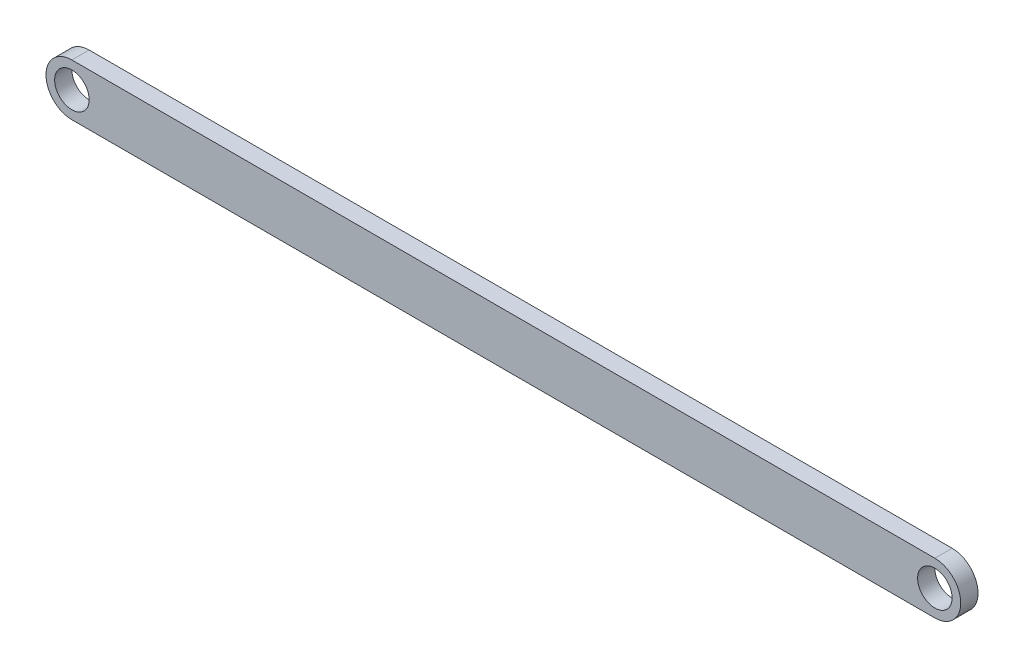
SolidWorks part; units mm, degrees
ref_plane "前视基准面" through (0, 0, 0) normal (0, 0, 1) x (1, 0, 0)
ref_plane "上视基准面" through (0, 0, 0) normal (0, 1, 0) x (1, 0, 0)
ref_plane "右视基准面" through (0, 0, 0) normal (1, 0, 0) x (0, 0, -1)
sketch "草图1" plane through (0, 0, 0) normal (0, 0, 1) x (1, 0, 0)
  line L1 (-51.9553, -3) -> (48.0447, -3)
  line L2 (-51.9553, 3) -> (48.0447, 3)
  arc A0 (48.0447, -3) -> (48.0447, 3) centre (48.0447, 0) ccw
  arc A1 (-51.9553, 3) -> (-51.9553, -3) centre (-51.9553, 0) ccw
  circle A2 centre (48.0447, 0) radius 2
  circle A3 centre (-51.9553, 0) radius 2
  dimension "D1" = 100
extrude "凸台-拉伸2" add sketch "草图1" along normal blind 2
